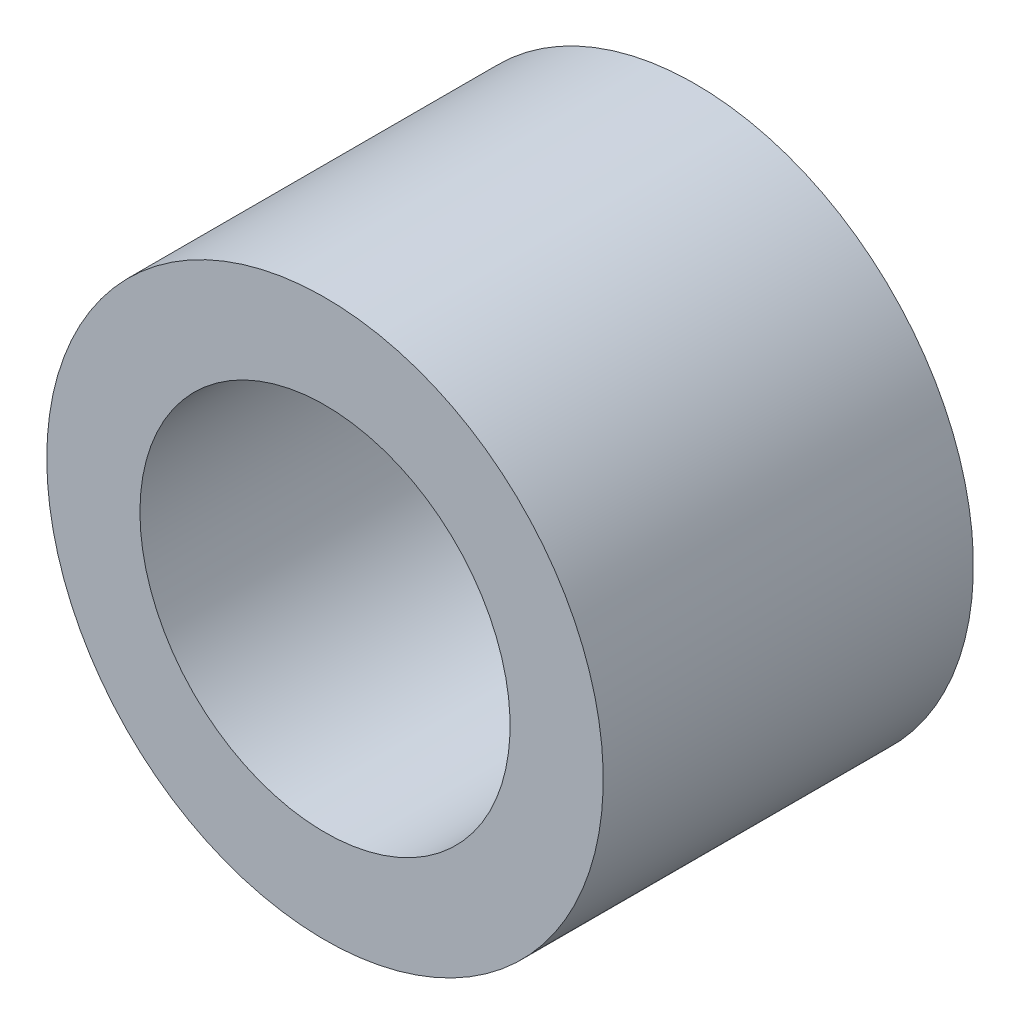
SolidWorks part; units mm, degrees
ref_plane "Front Plane" through (0, 0, 0) normal (0, 0, 1) x (1, 0, 0)
ref_plane "Top Plane" through (0, 0, 0) normal (0, 1, 0) x (1, 0, 0)
ref_plane "Right Plane" through (0, 0, 0) normal (1, 0, 0) x (0, 0, -1)
ref_plane "Plane1" through (0, 0, 0) normal (0, -1, 0) x (1, 0, 0)
sketch "Sketch1" plane through (0, 0, 0) normal (0, -1, 0) x (1, 0, 0)
  line L0 (4.51, 3) -> (3, 3)
  line L1 (3, 3) -> (3, -3)
  line L2 (3, -3) -> (4.51, -3)
  line L3 (4.51, -3) -> (4.51, 3)
  line L4 (0, 3) -> (0, -3) construction
revolve "Revolve1" add sketch "Sketch1" angle 360 about L4
